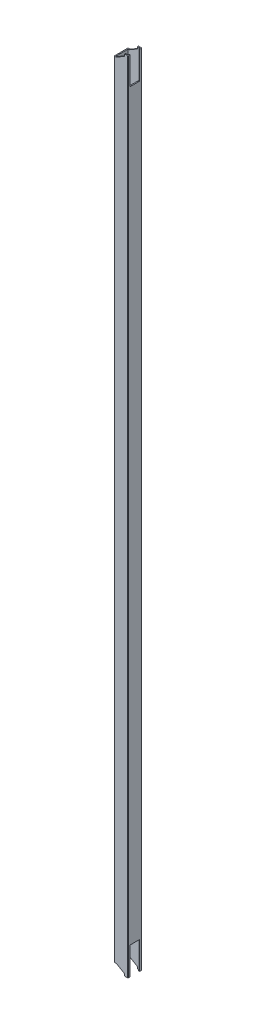
SolidWorks part; units mm, degrees
ref_plane "Front Plane" through (0, 0, 0) normal (0, 0, 1) x (1, 0, 0)
ref_plane "Top Plane" through (0, 0, 0) normal (0, 1, 0) x (1, 0, 0)
ref_plane "Right Plane" through (0, 0, 0) normal (1, 0, 0) x (0, 0, -1)
sketch "Sketch1" plane through (0, 0, 0) normal (0, 1, 0) x (1, 0, 0)
  line L0 (1.5, 1.5) -> (18.5, 1.5)
  line L1 (0.5, 0) -> (19.5, 0)
  line L2 (0, 0.5) -> (0, 19.5)
  line L3 (0.5, 20) -> (19.5, 20)
  line L4 (20, 0.5) -> (20, 19.5)
  line L5 (18.5, 1.5) -> (18.5, 18.5)
  line L6 (1.5, 18.5) -> (18.5, 18.5)
  line L7 (1.5, 1.5) -> (1.5, 18.5)
  arc A0 (19.5, 0) -> (20, 0.5) centre (19.5, 0.5) ccw
  arc A1 (0.5, 0) -> (0, 0.5) centre (0.5, 0.5) cw
  arc A2 (0, 19.5) -> (0.5, 20) centre (0.5, 19.5) cw
  arc A3 (19.5, 20) -> (20, 19.5) centre (19.5, 19.5) cw
  arc A4 (18.5, 1.5) -> (18.5, 1.5) centre (18.5, 1.5) ccw
  arc A5 (18.5, 18.5) -> (18.5, 18.5) centre (18.5, 18.5) cw
  arc A6 (1.5, 18.5) -> (1.5, 18.5) centre (1.5, 18.5) cw
  arc A7 (1.5, 1.5) -> (1.5, 1.5) centre (1.5, 1.5) cw
  point P9 (0, 0)
  dimension "D3" = 0.5
  dimension "D1" = 20
  dimension "D2" = 20
  dimension "D4" = 1.5
extrude "Boss-Extrude1" add sketch "Sketch1" along normal blind 1156.4
ref_plane "Plane1" through (0, 578.2, 0) normal (0, 1, 0) x (1, 0, 0)
sketch "Sketch5" plane through (0, 0, 0) normal (-1, 0, 0) x (0, 0, 1)
  line L0 (-1.5, 1156.4) -> (-18.5, 1156.4) construction
  line L16 (-17, 1156.4) -> (-3, 1156.4)
  line L17 (-17, 1156.4) -> (-17, 1116.4)
  line L18 (-17, 1116.4) -> (-3, 1116.4)
  line L19 (-3, 1156.4) -> (-3, 1116.4)
  point P7 (-10, 1156.4)
  point P8 (-10, 1156.4)
  dimension "D1" = 14
  dimension "D2" = 40
extrude "Cut-Extrude4" cut sketch "Sketch5" along normal blind 10 from offset 20 offset against normal yes
sketch "Sketch6" plane through (0, 0, -20) normal (0, 0, -1) x (-1, 0, 0)
  line L0 (-15, 1156.4) -> (-15, 1153.4)
  line L1 (-19.5, 1156.4) -> (-0.5, 1156.4) construction
  line L2 (-3, 1146.4) -> (0, 1146.4)
  line L3 (0, 1146.4) -> (0, 1156.4)
  line L4 (0, 1156.4) -> (-15, 1156.4)
  line L5 (0, 1156.4) -> (0, 0) construction
  line L6 (-15, 1153.4) -> (-3, 1146.4)
  dimension "D1" = 15
  dimension "D2" = 10
  dimension "D3" = 3
  dimension "D4" = 3
extrude "Cut-Extrude5" cut sketch "Sketch6" against normal through all
mirror "Mirror1" about plane through (0, 578.2, 0) normal (0, 1, 0) of "Cut-Extrude4", "Cut-Extrude5"
